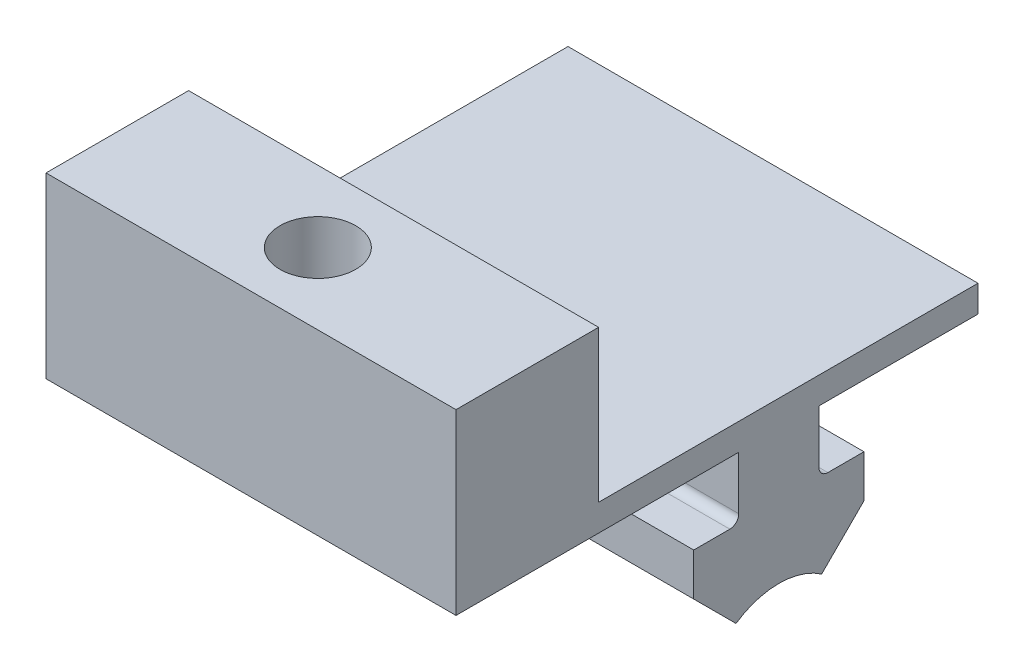
SolidWorks part; units mm, degrees
ref_plane "Front Plane" through (0, 0, 0) normal (0, 0, 1) x (1, 0, 0)
ref_plane "Top Plane" through (0, 0, 0) normal (0, 1, 0) x (1, 0, 0)
ref_plane "Right Plane" through (0, 0, 0) normal (1, 0, 0) x (0, 0, -1)
sketch "Sketch1" plane through (632.1, 0, 0) normal (1, 0, 0) x (0, 0, -1)
  line L72 (277.8, -589.1) -> (277.8, -586.1)
  line L73 (277.8, -586.1) -> (246.077, -586.1)
  line L74 (246.077, -586.1) -> (246.077, -566.1)
  line L75 (246.077, -566.1) -> (262.077, -566.1)
  line L76 (262.077, -566.1) -> (262.077, -583.1)
  line L77 (262.077, -583.1) -> (304.6431, -583.1)
  line L78 (304.6431, -583.1) -> (304.6431, -586.1)
  line L79 (304.6431, -586.1) -> (286.8, -586.1)
  line L80 (286.8, -592.075) -> (286.8, -589.1)
  line L81 (291.85, -593.075) -> (287.8, -593.075)
  line L82 (291.85, -597.8429) -> (291.85, -593.075)
  line L83 (287.1047, -602.5882) -> (291.85, -597.8429)
  line L84 (272.75, -597.8429) -> (277.4953, -602.5882)
  line L85 (272.75, -593.075) -> (272.75, -597.8429)
  line L86 (276.8, -593.075) -> (272.75, -593.075)
  line L87 (277.8, -589.1) -> (277.8, -592.075)
  line L88 (286.8, -592.075) -> (286.8, -589.1)
  line L89 (291.85, -593.075) -> (287.8, -593.075)
  line L90 (291.85, -597.8429) -> (291.85, -593.075)
  line L91 (287.1047, -602.5882) -> (291.85, -597.8429)
  line L92 (272.75, -597.8429) -> (277.4953, -602.5882)
  line L93 (272.75, -593.075) -> (272.75, -597.8429)
  line L94 (276.8, -593.075) -> (272.75, -593.075)
  line L95 (277.8, -589.1) -> (277.8, -592.075)
  line L96 (286.8, -586.1) -> (286.8, -589.1)
  line L97 (250.077, -77.1) -> (250.077, -577.1) construction
  line L98 (258.077, -577.1) -> (258.077, -77.1) construction
  arc A90 (286.8, -592.075) -> (287.8, -593.075) centre (287.8, -592.075) ccw
  arc A91 (287.1047, -602.5882) -> (277.4953, -602.5882) centre (282.3, -609.6) ccw
  arc A92 (276.8, -593.075) -> (277.8, -592.075) centre (276.8, -592.075) ccw
  arc A93 (286.8, -592.075) -> (287.8, -593.075) centre (287.8, -592.075) ccw
  arc A94 (287.1047, -602.5882) -> (277.4953, -602.5882) centre (282.3, -609.6) ccw
  arc A95 (276.8, -593.075) -> (277.8, -592.075) centre (276.8, -592.075) ccw
  dimension "D2" = 3
  dimension "D3" = 3
  dimension "D4" = 4
  dimension "D5" = 4
  dimension "D6" = 20
  dimension "D1" = 0.5
extrude "Boss-Extrude1" add sketch "Sketch1" against normal blind 46
sketch "Sketch2" plane through (0, -566.1, 0) normal (0, 1, 0) x (1, 0, 0)
  circle A0 centre (608.5985, 254.077) radius 4.25
extrude "Cut-Extrude1" cut sketch "Sketch2" against normal blind 10
